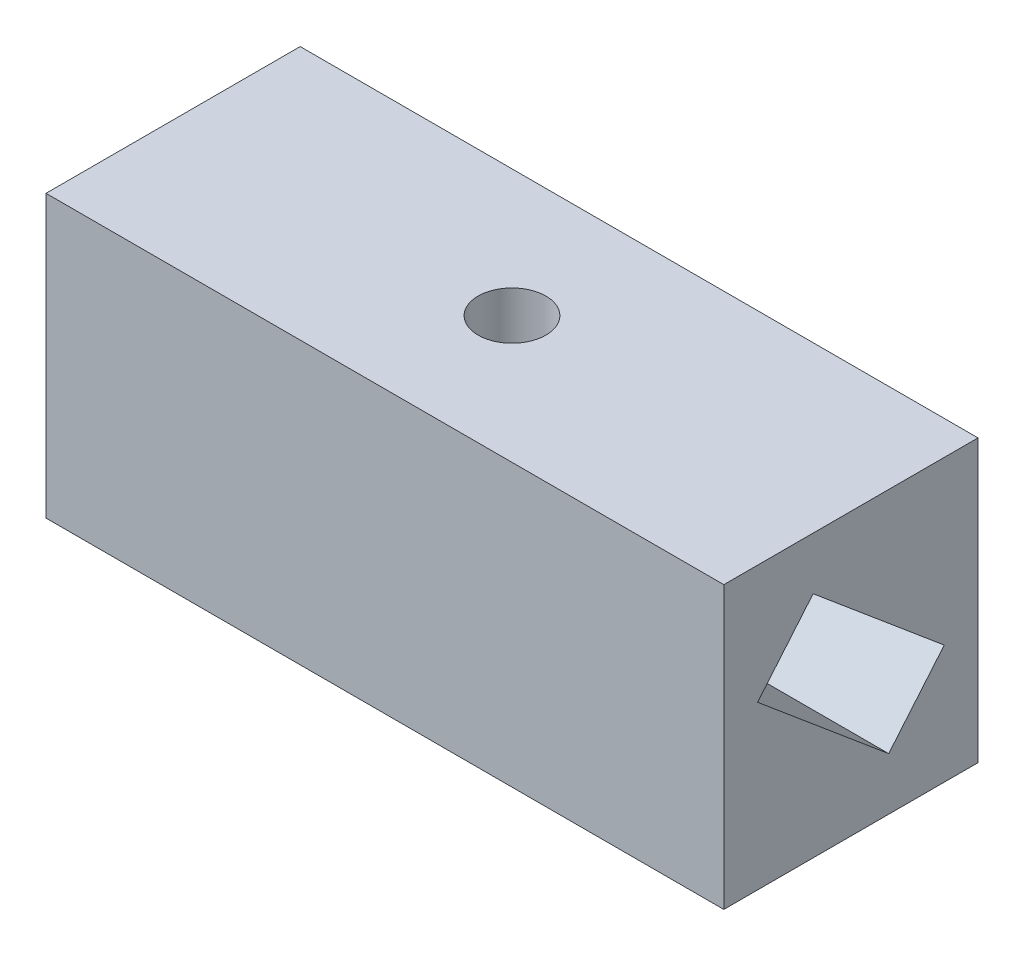
SolidWorks part; units mm, degrees
ref_plane "Спереди" through (0, 0, 0) normal (0, 0, 1) x (1, 0, 0)
ref_plane "Сверху" through (0, 0, 0) normal (0, 1, 0) x (1, 0, 0)
ref_plane "Справа" through (0, 0, 0) normal (1, 0, 0) x (0, 0, -1)
sketch "Эскиз1" plane through (0, 0, 0) normal (0, 1, 0) x (1, 0, 0)
  line L1 (-40, -15) -> (40, -15)
  line L2 (-40, -15) -> (-40, 15)
  line L3 (-40, 15) -> (40, 15)
  line L4 (40, -15) -> (40, 15)
  line L5 (-40, -15) -> (40, 15) construction
  line L6 (-40, 15) -> (40, -15) construction
  point P0 (0, 0)
  dimension "D1" = 80
  dimension "D2" = 30
extrude "Бобышка-Вытянуть1" add sketch "Эскиз1" along normal blind 33.2
sketch "Эскиз2" plane through (0, 33.2, 0) normal (0, 1, 0) x (1, 0, 0)
  line L0 (0, 15) -> (0, -15) construction
  line L1 (40, 15) -> (-40, 15) construction
  line L2 (-40, -15) -> (40, -15) construction
  circle A0 centre (0, 0) radius 4
  dimension "D1" = 8
extrude "Вырез-Вытянуть1" cut sketch "Эскиз2" against normal through all
sketch "Эскиз5" plane through (-40, 0, 0) normal (-1, 0, 0) x (0, 0, 1)
  line L0 (0, 33.2) -> (0, 0) construction
  line L2 (-15, 33.2) -> (15, 33.2) construction
  line L3 (15, 0) -> (-15, 33.2) construction
  line L4 (-11.0153, 14.0147) -> (-4.4588, 6.201)
  line L5 (-11.0153, 14.0147) -> (4.4588, 26.999)
  line L6 (4.4588, 26.999) -> (11.0153, 19.1853)
  line L7 (-4.4588, 6.201) -> (11.0153, 19.1853)
  line L8 (-11.0153, 14.0147) -> (11.0153, 19.1853) construction
  line L9 (4.4588, 26.999) -> (-4.4588, 6.201) construction
  point P5 (0, 16.6)
  point P6 (0, 16.6)
  dimension "D1" = 20.2
  dimension "D2" = 10.2
  dimension "D3" = 40
extrude "Вырез-Вытянуть4" cut sketch "Эскиз5" against normal blind 30
sketch "Эскиз6" plane through (40, 0, 0) normal (1, 0, 0) x (0, 0, -1)
  line L0 (0, 0) -> (0, 33.2) construction
  line L2 (-15, 33.2) -> (15, 33.2) construction
  line L3 (15, 0) -> (-15, 33.2) construction
  line L4 (11.0153, 14.0147) -> (4.4588, 6.201)
  line L5 (11.0153, 14.0147) -> (-4.4588, 26.999)
  line L6 (-4.4588, 26.999) -> (-11.0153, 19.1853)
  line L7 (4.4588, 6.201) -> (-11.0153, 19.1853)
  line L8 (11.0153, 14.0147) -> (-11.0153, 19.1853) construction
  line L9 (-4.4588, 26.999) -> (4.4588, 6.201) construction
  point P5 (0, 16.6)
  point P6 (0, 16.6)
  dimension "D1" = 10.2
  dimension "D2" = 20.2
  dimension "D3" = 40
extrude "Вырез-Вытянуть5" cut sketch "Эскиз6" against normal blind 30
